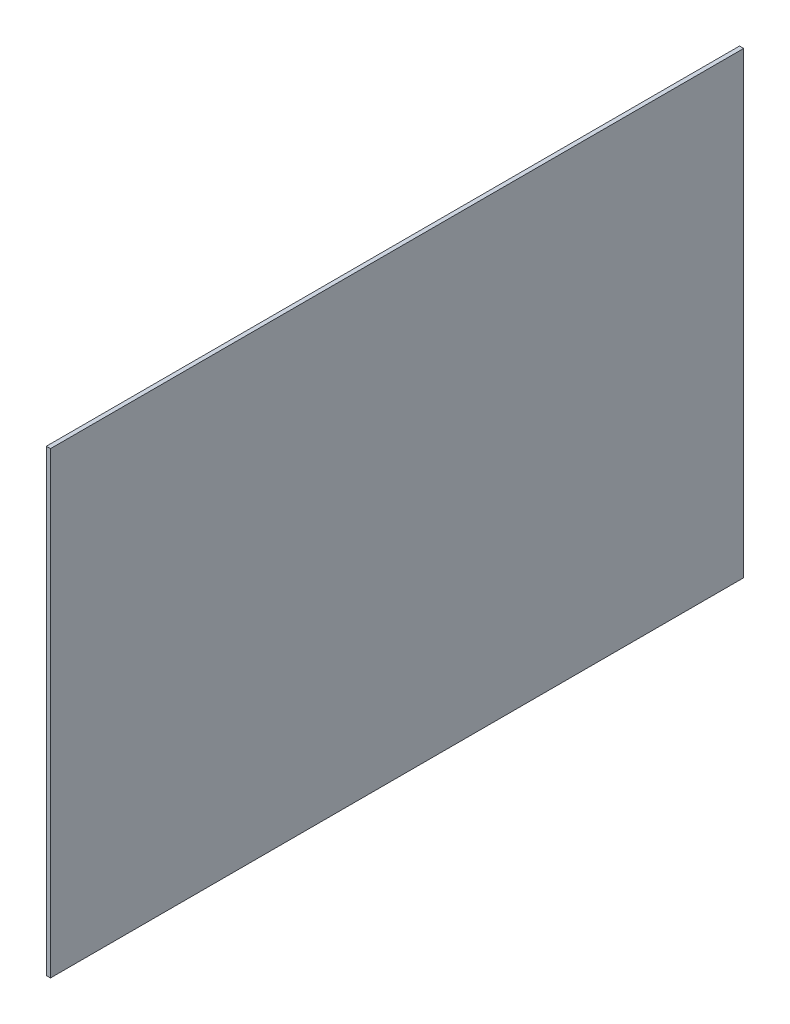
SolidWorks part; units mm, degrees
ref_plane "Front Plane" through (0, 0, 0) normal (0, 0, 1) x (1, 0, 0)
ref_plane "Top Plane" through (0, 0, 0) normal (0, 1, 0) x (1, 0, 0)
ref_plane "Right Plane" through (0, 0, 0) normal (1, 0, 0) x (0, 0, -1)
sketch "Sketch1" plane through (0, 0, 0) normal (1, 0, 0) x (0, 0, -1)
  line L0 (250, 145.3272) -> (250, 165.3272)
  line L1 (-250, -165.3272) -> (250, -165.3272)
  line L2 (250, -165.3272) -> (250, 145.3272)
  line L3 (250, 165.3272) -> (-250, 165.3272)
  line L4 (-250, 165.3272) -> (-250, -165.3272)
extrude "Boss-Extrude1" add sketch "Sketch1" along normal blind 3
